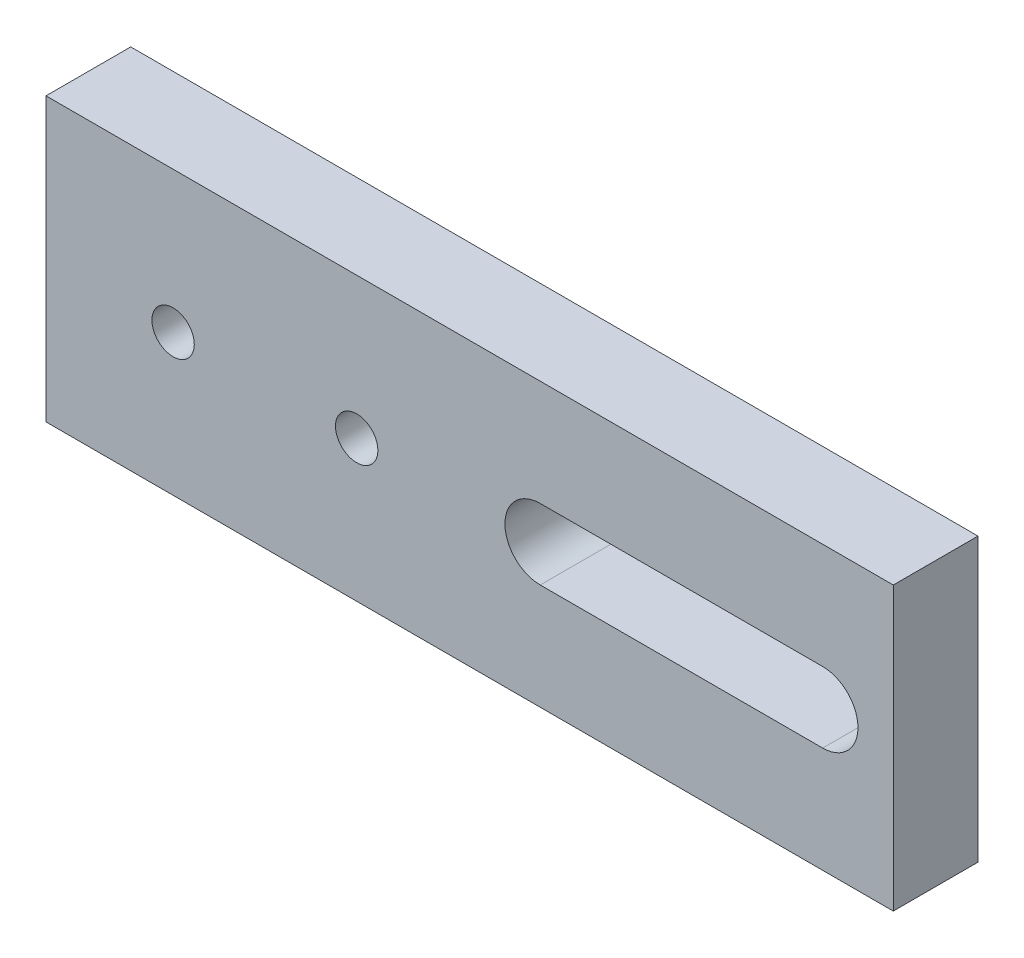
SolidWorks part; units mm, degrees
ref_plane "Front Plane" through (0, 0, 0) normal (0, 0, 1) x (1, 0, 0)
ref_plane "Top Plane" through (0, 0, 0) normal (0, 1, 0) x (1, 0, 0)
ref_plane "Right Plane" through (0, 0, 0) normal (1, 0, 0) x (0, 0, -1)
sketch "Sketch1" plane through (0, 0, 0) normal (0, 0, 1) x (1, 0, 0)
  line L0 (35, 10) -> (55, 10) construction
  line L1 (0, 0) -> (60, 0)
  line L2 (0, 0) -> (0, 20)
  line L3 (0, 20) -> (60, 20)
  line L4 (60, 0) -> (60, 20)
  line L5 (35, 12.5) -> (55, 12.5)
  line L6 (35, 7.5) -> (55, 7.5)
  arc A0 (35, 12.5) -> (35, 7.5) centre (35, 10) ccw
  arc A1 (55, 7.5) -> (55, 12.5) centre (55, 10) ccw
  circle A2 centre (22, 10) radius 1.5
  circle A3 centre (9, 10) radius 1.5
  point P7 (45, 10)
  point P12 (60, 10)
  dimension "D4" = 2.5
  dimension "D7" = 3
  dimension "D8" = 3
  dimension "D1" = 20
  dimension "D2" = 60
  dimension "D3" = 20
  dimension "D5" = 5
  dimension "D6" = 0
  dimension "D9" = 13
  dimension "D10" = 13
extrude "Boss-Extrude1" add sketch "Sketch1" along normal blind 6
